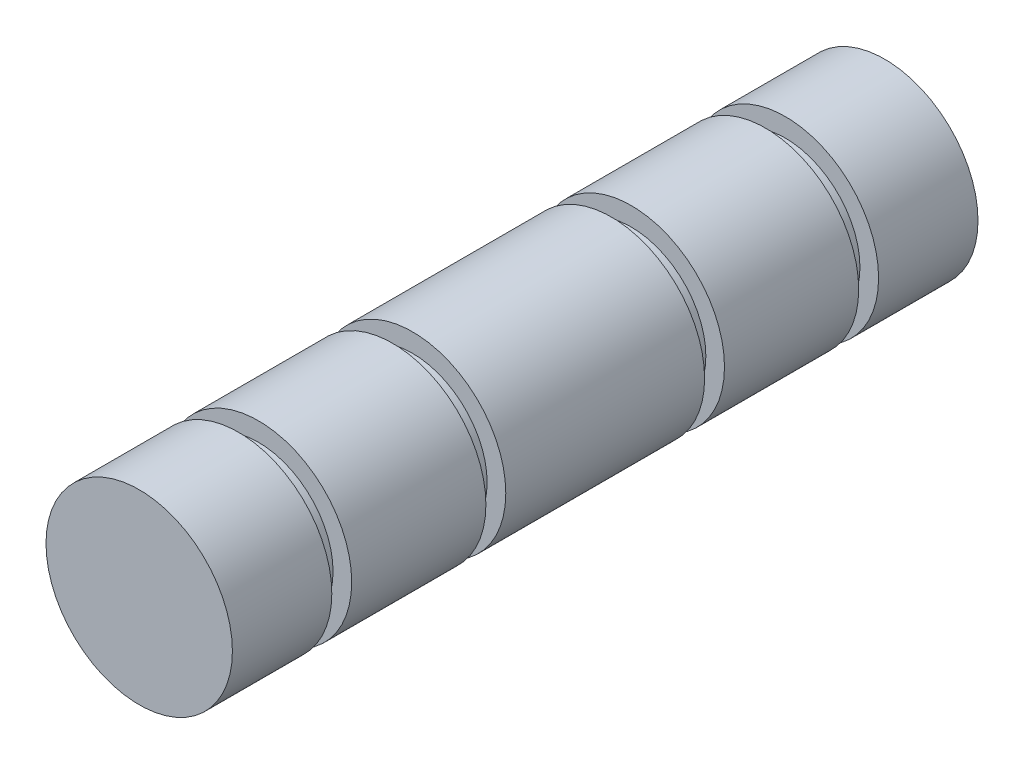
SolidWorks part; units mm, degrees
ref_plane "Front Plane" through (0, 0, 0) normal (0, 0, 1) x (1, 0, 0)
ref_plane "Top Plane" through (0, 0, 0) normal (0, 1, 0) x (1, 0, 0)
ref_plane "Right Plane" through (0, 0, 0) normal (1, 0, 0) x (0, 0, -1)
sketch "Sketch1" plane through (0, 0, 0) normal (0, 0, 1) x (1, 0, 0)
  circle A0 centre (0, 0) radius 4.7625
  dimension "D1" = 9.525
extrude "Boss-Extrude1" add sketch "Sketch1" along normal mid plane 38.1
sketch "Sketch2" plane through (0, 0, 0) normal (0, 1, 0) x (1, 0, 0)
  line L0 (4.7625, -19.05) -> (4.7625, 19.05) construction
  line L1 (4.7625, 13.97) -> (3.81, 13.97)
  line L2 (4.7625, 13.97) -> (4.7625, 12.954)
  line L3 (4.7625, 12.954) -> (3.81, 12.954)
  line L4 (3.81, 13.97) -> (3.81, 12.954)
  line L5 (4.7625, 19.05) -> (-4.7625, 19.05) construction
  line L6 (4.7625, -12.954) -> (3.81, -12.954)
  line L7 (4.7625, -12.954) -> (4.7625, -13.97)
  line L8 (4.7625, -13.97) -> (3.81, -13.97)
  line L9 (3.81, -12.954) -> (3.81, -13.97)
  line L10 (-4.7625, -19.05) -> (4.7625, -19.05) construction
  line L11 (4.7625, -19.05) -> (4.7625, 19.05) construction
  line L12 (4.7625, 6.096) -> (3.81, 6.096)
  line L13 (4.7625, 6.096) -> (4.7625, 5.08)
  line L14 (4.7625, 5.08) -> (3.81, 5.08)
  line L15 (3.81, 6.096) -> (3.81, 5.08)
  line L17 (4.7625, -5.08) -> (3.81, -5.08)
  line L18 (4.7625, -5.08) -> (4.7625, -6.096)
  line L19 (4.7625, -6.096) -> (3.81, -6.096)
  line L20 (3.81, -5.08) -> (3.81, -6.096)
  point P10 (3.81, 13.462)
  dimension "D1" = 0.9525
  dimension "D2" = 0.9525
  dimension "D3" = 1.016
  dimension "D4" = 1.016
  dimension "D5" = 5.08
  dimension "D6" = 5.08
  dimension "D7" = 0.9525
  dimension "D8" = 1.016
  dimension "D9" = 6.858
  dimension "D10" = 0.9525
  dimension "D11" = 1.016
  dimension "D12" = 6.858
ref_axis "Axis1" through (0, 0, 19.05) along (0, 0, -1)
revolve "Cut-Revolve1" cut sketch "Sketch2" angle 360 about axis through (0, 0, 19.05) along (0, 0, -1)
